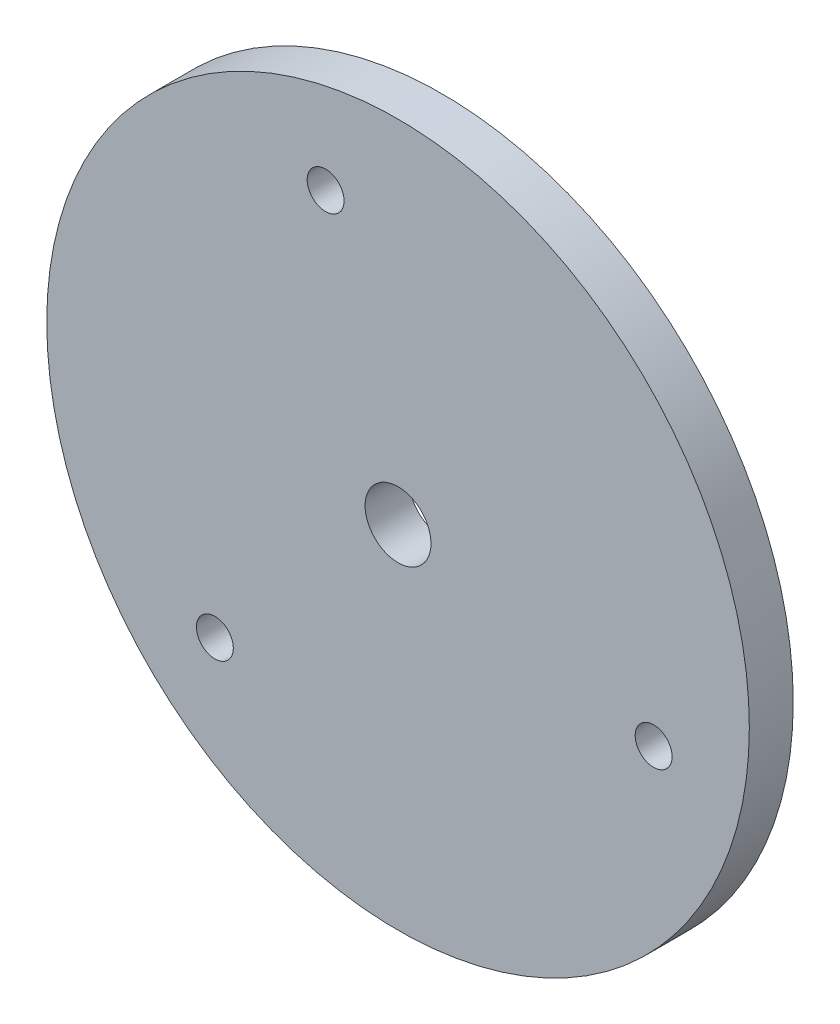
SolidWorks part; units mm, degrees
ref_plane "Front" through (0, 0, 0) normal (0, 0, 1) x (1, 0, 0)
ref_plane "Top" through (0, 0, 0) normal (0, 1, 0) x (1, 0, 0)
ref_plane "Right" through (0, 0, 0) normal (1, 0, 0) x (0, 0, -1)
sketch "Sketch1" plane through (0, 0, 0) normal (0, 0, 1) x (1, 0, 0)
  line L1 (36.9609, -9.2468) -> (-10.4725, 36.6325) construction
  line L2 (-10.4725, 36.6325) -> (-26.4884, -27.3857) construction
  line L3 (-26.4884, -27.3857) -> (36.9609, -9.2468) construction
  circle A0 centre (0, 0) radius 50.8
  circle A1 centre (0, 0) radius 19.05 construction
  circle A2 centre (-10.4725, 36.6325) radius 2.667
  circle A3 centre (36.9609, -9.2468) radius 2.667
  circle A4 centre (-26.4884, -27.3857) radius 2.667
  circle A6 centre (0, 0) radius 4.7625
  dimension "D1" = 38.1
  dimension "D2" = 5.334
  dimension "D3" = 101.6
  dimension "D4" = 9.525
extrude "Boss-Extrude1" add sketch "Sketch1" along normal blind 6.35
